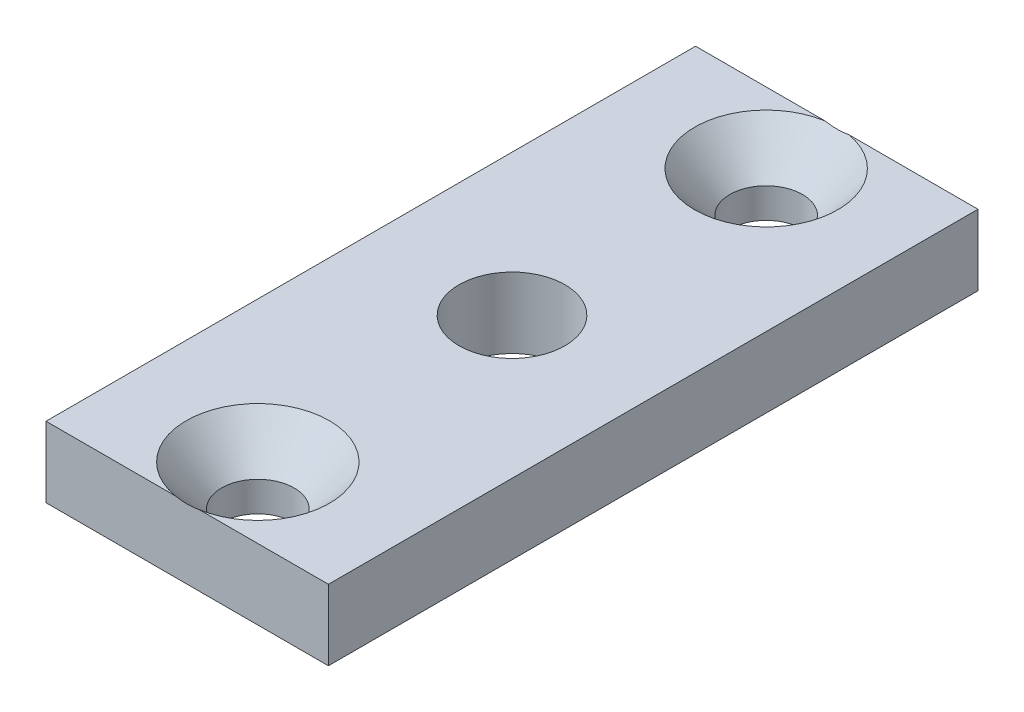
SolidWorks part; units mm, degrees
material "Alloy Steel"
ref_plane "Front Plane" through (0, 0, 0) normal (0, 0, 1) x (1, 0, 0)
ref_plane "Top Plane" through (0, 0, 0) normal (0, 1, 0) x (1, 0, 0)
ref_plane "Right Plane" through (0, 0, 0) normal (1, 0, 0) x (0, 0, -1)
sketch "Sketch1" plane through (0, 0, 0) normal (0, 0, 1) x (1, 0, 0)
  line L0 (-12.7, -3.175) -> (12.7, -3.175)
  line L1 (-12.7, -3.175) -> (-12.7, 3.175)
  line L2 (12.7, -3.175) -> (12.7, 3.175)
  line L3 (-12.7, 3.175) -> (12.7, 3.175)
  line L4 (-12.7, -3.175) -> (12.7, 3.175) construction
  line L5 (12.7, -3.175) -> (-12.7, 3.175) construction
  point P1 (0, 0)
  dimension "D1" = 25.4
  dimension "D2" = 6.35
extrude "Extrude1" add sketch "Sketch1" along normal blind 58.42
sketch "Sketch2" plane through (0, 3.175, 0) normal (0, 1, 0) x (1, 0, 0)
  line L0 (0, 0) -> (0, -6.35) construction
  line L1 (0, -58.42) -> (0, -52.07) construction
  line L2 (12.7, -58.42) -> (-12.7, -58.42) construction
  line L3 (-12.7, -29.21) -> (12.7, -29.21) construction
  line L4 (-12.7, -58.42) -> (-12.7, 0) construction
  line L5 (12.7, -58.42) -> (12.7, 0) construction
  line L6 (0, -29.21) -> (0, -40.259) construction
  point P13 (0, -29.21)
  dimension "D1" = 45.72
  dimension "D2" = 11.049
  dimension "D3" = 6.35
hole_wizard "CSK for 1/4 Flat Head Machine Screw1" positions "3DSketch1" profile "Sketch3" countersink size "1/4" standard "Ansi Inch" end condition through all
sketch3d "3DSketch1"
  point P0 (0, 3.175, 6.35)
  point P4 (0, 3.175, 52.07)
sketch "Sketch3" plane through (0, 3.175, 6.35) normal (1, 0, 0) x (0, 0, 1)
  line L0 (0, 0) -> (0, 6.35)
  line L1 (0, 6.35) -> (3.2639, 6.35)
  line L2 (3.2639, 6.35) -> (3.2639, 3.6524)
  line L3 (3.2639, 3.6524) -> (6.4389, 0)
  line L5 (6.4389, 0) -> (0, 0)
  line L6 (-3.2639, 3.6524) -> (-6.4389, 0) construction
  line L11 (0, -6.35) -> (0, 107.95) construction
  dimension "Thru Hole Dia." = 6.5278
  dimension "Thru Hole Depth" = 6.35
  dimension "Near C'Sink Dia." = 12.8778
  dimension "Near C'Sink Angle" = 82
hole_wizard "3/8 (0.375) Diameter Hole1" positions "3DSketch3" profile "Sketch5" hole size "3/8" standard "Ansi Inch" end condition through all
sketch3d "3DSketch3"
  point P0 (0, 3.175, 29.21)
sketch "Sketch5" plane through (0, 3.175, 29.21) normal (1, 0, 0) x (0, 0, 1)
  line L0 (0, 0) -> (0, 6.35)
  line L1 (0, 6.35) -> (4.7625, 6.35)
  line L2 (4.7625, 6.35) -> (4.7625, 0)
  line L5 (4.7625, 0) -> (0, 0)
  line L11 (0, -6.35) -> (0, 107.95) construction
  dimension "Thru Hole Dia." = 9.525
  dimension "Thru Hole Depth" = 6.35
